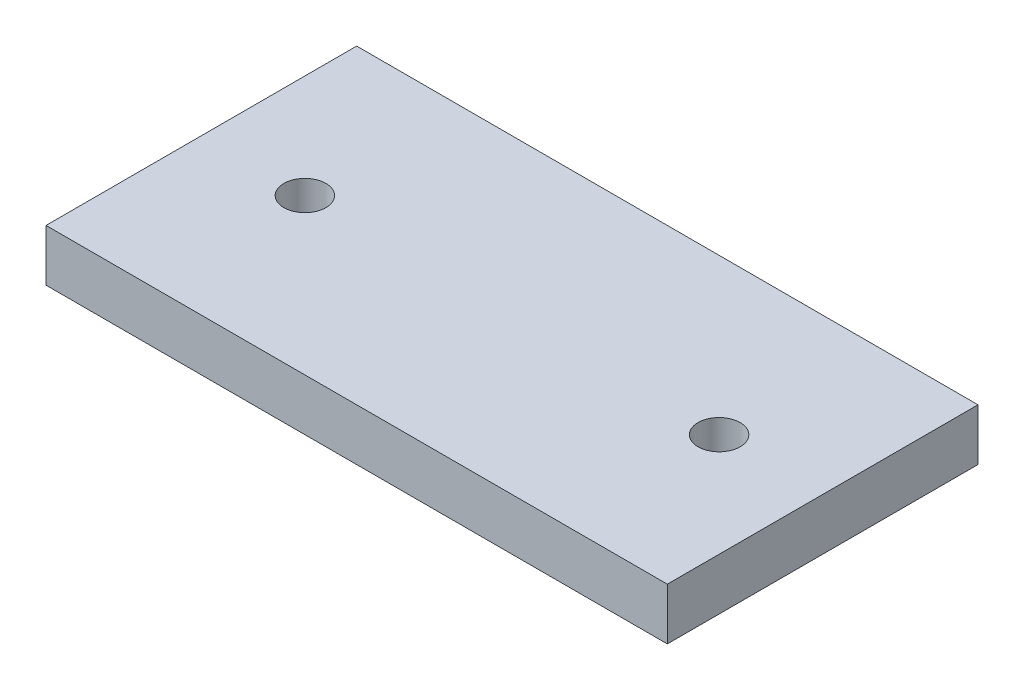
SolidWorks part; units mm, degrees
ref_plane "Front Plane" through (0, 0, 0) normal (0, 0, 1) x (1, 0, 0)
ref_plane "Top Plane" through (0, 0, 0) normal (0, 1, 0) x (1, 0, 0)
ref_plane "Right Plane" through (0, 0, 0) normal (1, 0, 0) x (0, 0, -1)
sketch "Sketch1" plane through (0, 0, 0) normal (0, 1, 0) x (1, 0, 0)
  line L0 (0, 76.2) -> (304.8, 76.2) construction
  line L1 (0, 0) -> (304.8, 0)
  line L2 (0, 0) -> (0, 152.4)
  line L3 (0, 152.4) -> (304.8, 152.4)
  line L4 (304.8, 0) -> (304.8, 152.4)
  line L11 (152.4, 152.4) -> (152.4, 0) construction
  circle A0 centre (50.8, 76.2) radius 10.3188
  circle A1 centre (254, 76.2) radius 10.3187
  dimension "D3" = 20.6375
  dimension "D4" = 50.8
  dimension "D5" = 50.8
  dimension "D1" = 152.4
  dimension "D2" = 304.8
extrude "Boss-Extrude1" add sketch "Sketch1" along normal blind 25.4
